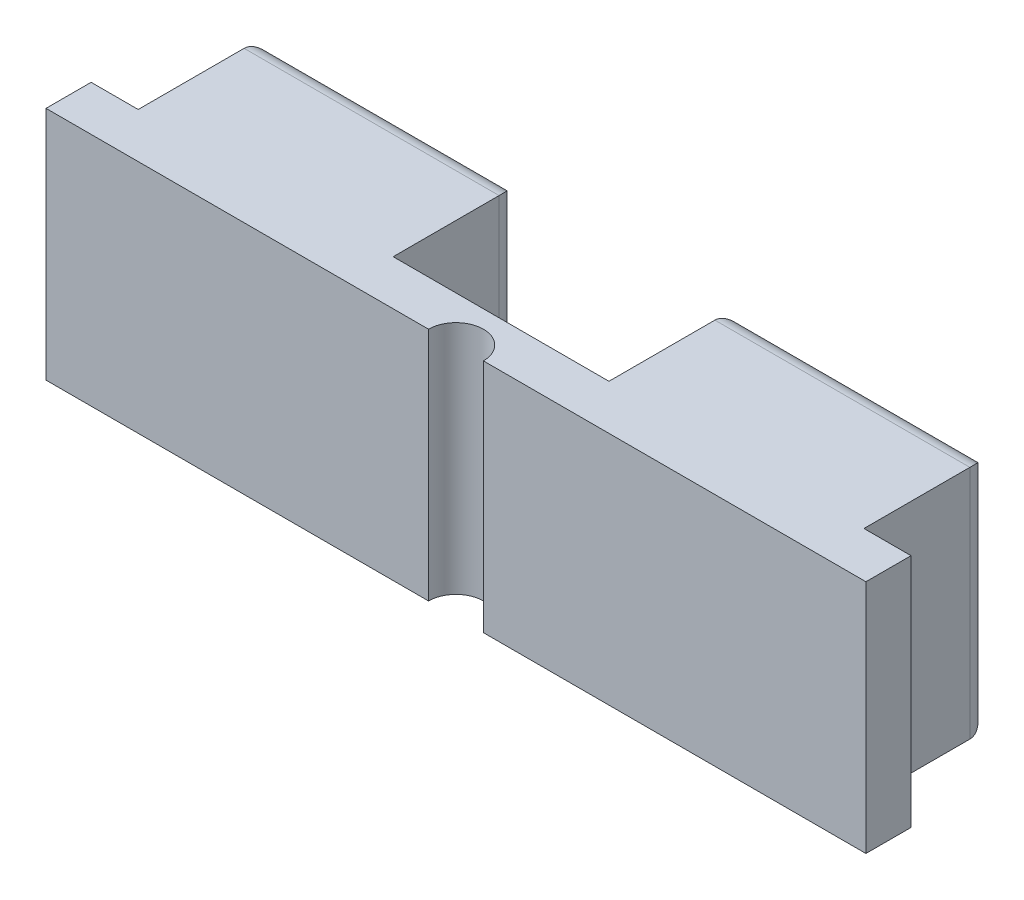
SolidWorks part; units mm, degrees
ref_plane "前视基准面" through (0, 0, 0) normal (0, 0, 1) x (1, 0, 0)
ref_plane "上视基准面" through (0, 0, 0) normal (0, 1, 0) x (1, 0, 0)
ref_plane "右视基准面" through (0, 0, 0) normal (1, 0, 0) x (0, 0, -1)
sketch "草图1" plane through (0, 0, 0) normal (0, 1, 0) x (1, 0, 0)
  line L2 (-153.7477, 90.1413) -> (-154.9477, 90.1413)
  line L3 (-153.7477, 92.3413) -> (-153.7477, 93.3413)
  line L4 (-153.7477, 93.3413) -> (-147.2477, 93.3413)
  line L5 (-147.2477, 93.3413) -> (-147.2477, 90.1413)
  line L6 (-147.2477, 90.1413) -> (-141.9977, 90.1413)
  line L7 (-141.9977, 90.1413) -> (-141.7477, 90.1413)
  line L8 (-141.7477, 90.1413) -> (-141.7477, 93.3413)
  line L9 (-141.7477, 93.3413) -> (-135.2477, 93.3413)
  line L10 (-135.2477, 93.3413) -> (-135.2477, 90.1413)
  line L11 (-135.2477, 90.1413) -> (-134.0477, 90.1413)
  line L12 (-134.0477, 90.1413) -> (-134.0477, 89.3413)
  line L14 (-154.9477, 90.1413) -> (-154.9477, 89.3413)
  line L19 (-153.7477, 90.1413) -> (-153.7477, 92.3413)
  line L33 (-134.0477, 88.9913) -> (-134.0477, 89.3413)
  line L34 (-154.9477, 89.3413) -> (-154.9477, 88.9913)
  line L35 (-154.9477, 88.9913) -> (-134.0477, 88.9913)
  arc A0 (-143.7977, 88.9913) -> (-145.1977, 88.9913) centre (-144.4977, 88.9913) ccw
extrude "凸台-拉伸1" add sketch "草图1" along normal blind 6
sketch "草图2" plane through (0, 0, -93.3413) normal (0, 0, -1) x (-1, 0, 0)
  line L0 (135.2477, 3) -> (141.7477, 3)
  line L1 (135.2477, 6) -> (135.2477, 0) construction
  line L2 (141.7477, 6) -> (141.7477, 0) construction
  line L3 (147.2477, 3) -> (153.7477, 3)
  line L4 (147.2477, 6) -> (147.2477, 0) construction
  line L5 (153.7477, 6) -> (153.7477, 0) construction
  line L6 (138.4977, 3) -> (138.4977, 1.2)
  line L7 (138.4977, 1.2) -> (137.9977, 1.2)
  line L8 (137.9977, 1.2) -> (137.9977, 4.8)
  line L9 (137.9977, 4.8) -> (138.9977, 4.8)
  line L10 (138.9977, 4.8) -> (138.9977, 1.2)
  line L11 (138.9977, 1.2) -> (138.4977, 1.2)
  line L12 (138.4977, 3) -> (138.4977, 2.5)
  line L13 (138.4977, 2.5) -> (140.2977, 2.5)
  line L14 (140.2977, 2.5) -> (140.2977, 3.5)
  line L15 (140.2977, 3.5) -> (136.6977, 3.5)
  line L16 (136.6977, 3.5) -> (136.6977, 2.5)
  line L17 (136.6977, 2.5) -> (138.4977, 2.5)
  line L18 (150.4977, 3) -> (150.4977, 2.5)
  line L19 (150.4977, 2.5) -> (152.2977, 2.5)
  line L20 (152.2977, 2.5) -> (152.2977, 3.5)
  line L21 (152.2977, 3.5) -> (148.6977, 3.5)
  line L22 (148.6977, 3.5) -> (148.6977, 2.5)
  line L23 (148.6977, 2.5) -> (150.4977, 2.5)
extrude "切除-拉伸1" cut sketch "草图2" against normal blind 0.5 contours L21 L22 L3 L20 | L19 L20 L3 L18 | L22 L23 L18 L3 | L15 L10 L9 L8 | L15 L16 L0 L8 | L10 L15 L8 L0 | L14 L15 L10 L0 | L13 L14 L0 L10 | L6 L13 L10 L0 | L8 L17 L6 L0 | L16 L17 L8 L0 | L17 L8 L7 L6 | L13 L6 L11 L10
fillet "圆角1" radius 0.5 8 edges at (-150.4977, 6, -93.3413) (-153.7477, 3, -93.3413) (-150.4977, 0, -93.3413) (-147.2477, 3, -93.3413) (-141.7477, 3, -93.3413) (-138.4977, 0, -93.3413) (-135.2477, 3, -93.3413) (-138.4977, 6, -93.3413)
